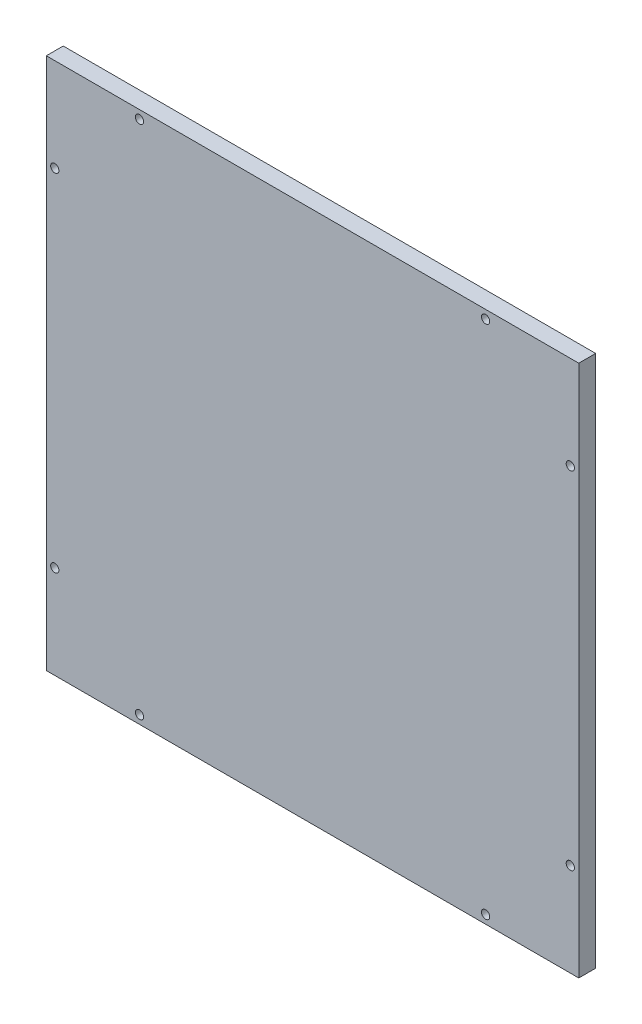
SolidWorks part; units mm, degrees
ref_plane "Front" through (0, 0, 0) normal (0, 0, 1) x (1, 0, 0)
ref_plane "Top" through (0, 0, 0) normal (0, 1, 0) x (1, 0, 0)
ref_plane "Right" through (0, 0, 0) normal (1, 0, 0) x (0, 0, -1)
sketch "Sketch1" plane through (0, 0, 0) normal (0, 0, 1) x (1, 0, 0)
  line L1 (-100, -100) -> (100, -100)
  line L2 (-100, -100) -> (-100, 100)
  line L3 (-100, 100) -> (100, 100)
  line L4 (100, -100) -> (100, 100)
  line L5 (-100, -100) -> (100, 100) construction
  line L6 (-100, 100) -> (100, -100) construction
  point P0 (0, 0)
  dimension "D1" = 200
  dimension "D2" = 200
extrude "Boss-Extrude1" add sketch "Sketch1" along normal blind 6.35
sketch "Sketch2" plane through (0, 0, 6.35) normal (0, 0, 1) x (1, 0, 0)
  line L0 (-100, 100) -> (100, 100) construction
  line L1 (-100, 100) -> (-100, 93.65) construction
  line L2 (-100, 93.65) -> (100, 93.65) construction
  line L3 (100, 100) -> (100, 93.65) construction
  line L4 (0, 100) -> (0, 93.65) construction
  line L5 (-100, 0) -> (100, 0) construction
  line L6 (100, 100) -> (93.65, 100) construction
  line L7 (100, 100) -> (100, -100) construction
  line L8 (100, -100) -> (93.65, -100) construction
  line L9 (93.65, 100) -> (93.65, -100) construction
  line L10 (0, 93.65) -> (0, -93.65) construction
  circle A0 centre (-65, 96.825) radius 1.55
  circle A1 centre (65, 96.825) radius 1.55
  circle A2 centre (65, -96.825) radius 1.55
  circle A3 centre (-65, -96.825) radius 1.55
  circle A4 centre (96.825, 65) radius 1.55
  circle A5 centre (96.825, -65) radius 1.55
  circle A6 centre (-96.825, -65) radius 1.55
  circle A7 centre (-96.825, 65) radius 1.55
  point P9 (0, 96.825)
extrude "Cut-Extrude1" cut sketch "Sketch2" against normal through all
